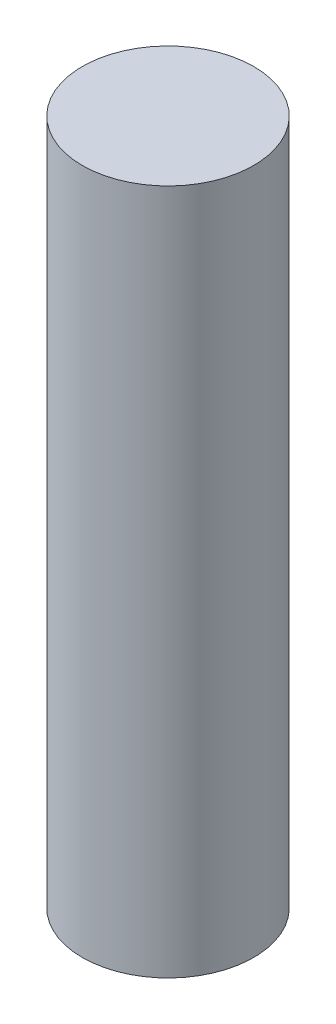
SolidWorks part; units mm, degrees
ref_plane "Front Plane" through (0, 0, 0) normal (0, 0, 1) x (1, 0, 0)
ref_plane "Top Plane" through (0, 0, 0) normal (0, 1, 0) x (1, 0, 0)
ref_plane "Right Plane" through (0, 0, 0) normal (1, 0, 0) x (0, 0, -1)
sketch "Sketch1" plane through (0, 0, 0) normal (0, 1, 0) x (1, 0, 0)
  circle A0 centre (0, 0) radius 5
  dimension "D1" = 10
extrude "Boss-Extrude1" add sketch "Sketch1" along normal mid plane 40
